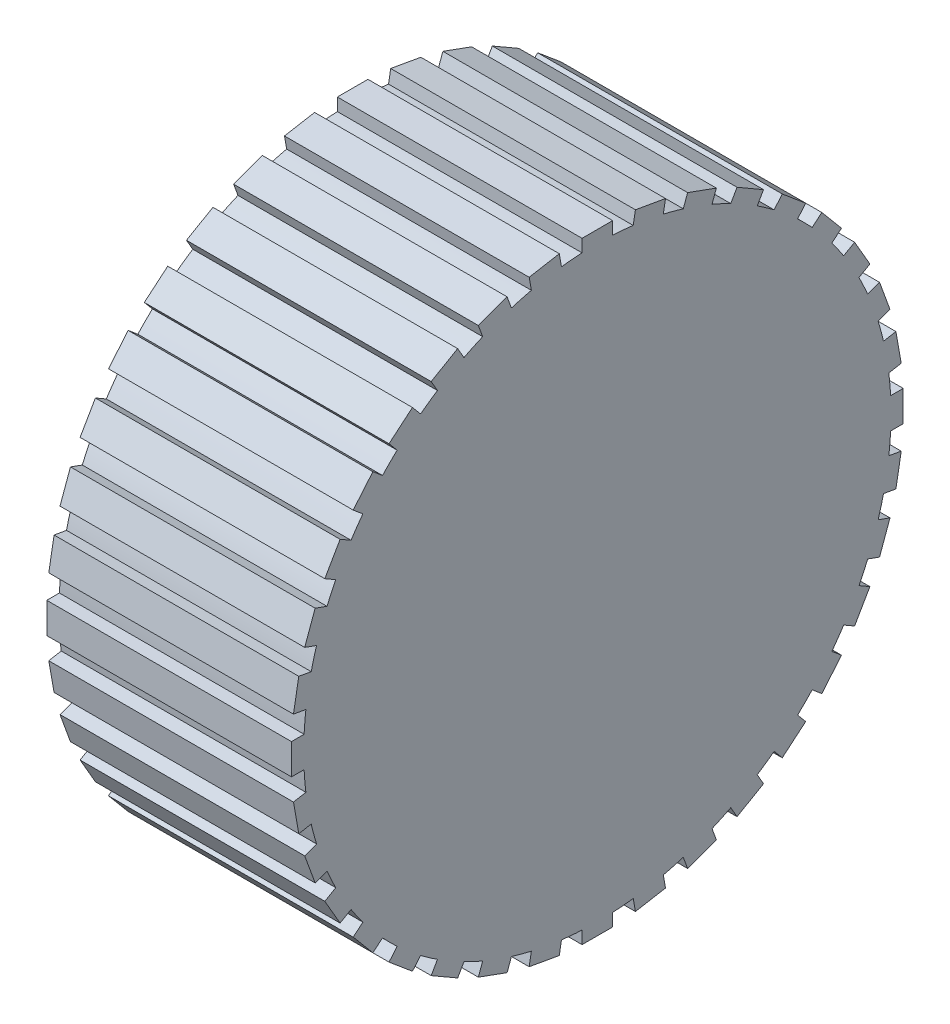
SolidWorks part; units mm, degrees
ref_plane "Front Plane" through (0, 0, 0) normal (0, 0, 1) x (1, 0, 0)
ref_plane "Top Plane" through (0, 0, 0) normal (0, 1, 0) x (1, 0, 0)
ref_plane "Right Plane" through (0, 0, 0) normal (1, 0, 0) x (0, 0, -1)
sketch "Sketch1" plane through (0, 0, 0) normal (1, 0, 0) x (0, 0, -1)
  line L0 (0, 0) -> (0, 250) construction
  line L1 (-12.5, 250) -> (12.5, 250)
  line L2 (-12.5, 250) -> (-12.5, 239.6743)
  line L3 (12.5, 250) -> (12.5, 239.6743)
  line L4 (31.1019, 248.3725) -> (55.7221, 244.0313)
  line L5 (31.1019, 248.3725) -> (29.3089, 238.2037)
  line L6 (55.7221, 244.0313) -> (53.9291, 233.8625)
  line L7 (73.7589, 239.1984) -> (97.2512, 230.6479)
  line L8 (73.7589, 239.1984) -> (70.2273, 229.4954)
  line L9 (97.2512, 230.6479) -> (93.7196, 220.9449)
  line L10 (114.1747, 222.7564) -> (135.8253, 210.2564)
  line L11 (114.1747, 222.7564) -> (109.0118, 213.814)
  line L12 (135.8253, 210.2564) -> (130.6624, 201.314)
  line L13 (151.1213, 199.546) -> (170.2725, 183.4763)
  line L14 (151.1213, 199.546) -> (144.4841, 191.636)
  line L15 (170.2725, 183.4763) -> (163.6352, 175.5663)
  line L16 (183.4763, 170.2725) -> (199.546, 151.1213)
  line L17 (183.4763, 170.2725) -> (175.5663, 163.6352)
  line L18 (199.546, 151.1213) -> (191.636, 144.4841)
  line L19 (210.2564, 135.8253) -> (222.7564, 114.1747)
  line L20 (210.2564, 135.8253) -> (201.314, 130.6624)
  line L21 (222.7564, 114.1747) -> (213.814, 109.0118)
  line L22 (230.6479, 97.2512) -> (239.1984, 73.7589)
  line L23 (230.6479, 97.2512) -> (220.9449, 93.7196)
  line L24 (239.1984, 73.7589) -> (229.4954, 70.2273)
  line L25 (244.0313, 55.7221) -> (248.3725, 31.1019)
  line L26 (244.0313, 55.7221) -> (233.8625, 53.9291)
  line L27 (248.3725, 31.1019) -> (238.2037, 29.3089)
  line L28 (250, 12.5) -> (250, -12.5)
  line L29 (250, 12.5) -> (239.6743, 12.5)
  line L30 (250, -12.5) -> (239.6743, -12.5)
  line L31 (248.3725, -31.1019) -> (244.0313, -55.7221)
  line L32 (248.3725, -31.1019) -> (238.2037, -29.3089)
  line L33 (244.0313, -55.7221) -> (233.8625, -53.9291)
  line L34 (239.1984, -73.7589) -> (230.6479, -97.2512)
  line L35 (239.1984, -73.7589) -> (229.4954, -70.2273)
  line L36 (230.6479, -97.2512) -> (220.9449, -93.7196)
  line L37 (222.7564, -114.1747) -> (210.2564, -135.8253)
  line L38 (222.7564, -114.1747) -> (213.814, -109.0118)
  line L39 (210.2564, -135.8253) -> (201.314, -130.6624)
  line L40 (199.546, -151.1213) -> (183.4763, -170.2725)
  line L41 (199.546, -151.1213) -> (191.636, -144.4841)
  line L42 (183.4763, -170.2725) -> (175.5663, -163.6352)
  line L43 (170.2725, -183.4763) -> (151.1213, -199.546)
  line L44 (170.2725, -183.4763) -> (163.6352, -175.5663)
  line L45 (151.1213, -199.546) -> (144.4841, -191.636)
  line L46 (135.8253, -210.2564) -> (114.1747, -222.7564)
  line L47 (135.8253, -210.2564) -> (130.6624, -201.314)
  line L48 (114.1747, -222.7564) -> (109.0118, -213.814)
  line L49 (97.2512, -230.6479) -> (73.7589, -239.1984)
  line L50 (97.2512, -230.6479) -> (93.7196, -220.9449)
  line L51 (73.7589, -239.1984) -> (70.2273, -229.4954)
  line L52 (55.7221, -244.0313) -> (31.1019, -248.3725)
  line L53 (55.7221, -244.0313) -> (53.9291, -233.8625)
  line L54 (31.1019, -248.3725) -> (29.3089, -238.2037)
  line L55 (12.5, -250) -> (-12.5, -250)
  line L56 (12.5, -250) -> (12.5, -239.6743)
  line L57 (-12.5, -250) -> (-12.5, -239.6743)
  line L58 (-31.1019, -248.3725) -> (-55.7221, -244.0313)
  line L59 (-31.1019, -248.3725) -> (-29.3089, -238.2037)
  line L60 (-55.7221, -244.0313) -> (-53.9291, -233.8625)
  line L61 (-73.7589, -239.1984) -> (-97.2512, -230.6479)
  line L62 (-73.7589, -239.1984) -> (-70.2273, -229.4954)
  line L63 (-97.2512, -230.6479) -> (-93.7196, -220.9449)
  line L64 (-114.1747, -222.7564) -> (-135.8253, -210.2564)
  line L65 (-114.1747, -222.7564) -> (-109.0118, -213.814)
  line L66 (-135.8253, -210.2564) -> (-130.6624, -201.314)
  line L67 (-151.1213, -199.546) -> (-170.2725, -183.4763)
  line L68 (-151.1213, -199.546) -> (-144.4841, -191.636)
  line L69 (-170.2725, -183.4763) -> (-163.6352, -175.5663)
  line L70 (-183.4763, -170.2725) -> (-199.546, -151.1213)
  line L71 (-183.4763, -170.2725) -> (-175.5663, -163.6352)
  line L72 (-199.546, -151.1213) -> (-191.636, -144.4841)
  line L73 (-210.2564, -135.8253) -> (-222.7564, -114.1747)
  line L74 (-210.2564, -135.8253) -> (-201.314, -130.6624)
  line L75 (-222.7564, -114.1747) -> (-213.814, -109.0118)
  line L76 (-230.6479, -97.2512) -> (-239.1984, -73.7589)
  line L77 (-230.6479, -97.2512) -> (-220.9449, -93.7196)
  line L78 (-239.1984, -73.7589) -> (-229.4954, -70.2273)
  line L79 (-244.0313, -55.7221) -> (-248.3725, -31.1019)
  line L80 (-244.0313, -55.7221) -> (-233.8625, -53.9291)
  line L81 (-248.3725, -31.1019) -> (-238.2037, -29.3089)
  line L82 (-250, -12.5) -> (-250, 12.5)
  line L83 (-250, -12.5) -> (-239.6743, -12.5)
  line L84 (-250, 12.5) -> (-239.6743, 12.5)
  line L85 (-248.3725, 31.1019) -> (-244.0313, 55.7221)
  line L86 (-248.3725, 31.1019) -> (-238.2037, 29.3089)
  line L87 (-244.0313, 55.7221) -> (-233.8625, 53.9291)
  line L88 (-239.1984, 73.7589) -> (-230.6479, 97.2512)
  line L89 (-239.1984, 73.7589) -> (-229.4954, 70.2273)
  line L90 (-230.6479, 97.2512) -> (-220.9449, 93.7196)
  line L91 (-222.7564, 114.1747) -> (-210.2564, 135.8253)
  line L92 (-222.7564, 114.1747) -> (-213.814, 109.0118)
  line L93 (-210.2564, 135.8253) -> (-201.314, 130.6624)
  line L94 (-199.546, 151.1213) -> (-183.4763, 170.2725)
  line L95 (-199.546, 151.1213) -> (-191.636, 144.4841)
  line L96 (-183.4763, 170.2725) -> (-175.5663, 163.6352)
  line L97 (-170.2725, 183.4763) -> (-151.1213, 199.546)
  line L98 (-170.2725, 183.4763) -> (-163.6352, 175.5663)
  line L99 (-151.1213, 199.546) -> (-144.4841, 191.636)
  line L100 (-135.8253, 210.2564) -> (-114.1747, 222.7564)
  line L101 (-135.8253, 210.2564) -> (-130.6624, 201.314)
  line L102 (-114.1747, 222.7564) -> (-109.0118, 213.814)
  line L103 (-97.2512, 230.6479) -> (-73.7589, 239.1984)
  line L104 (-97.2512, 230.6479) -> (-93.7196, 220.9449)
  line L105 (-73.7589, 239.1984) -> (-70.2273, 229.4954)
  line L106 (-55.7221, 244.0313) -> (-31.1019, 248.3725)
  line L107 (-55.7221, 244.0313) -> (-53.9291, 233.8625)
  line L108 (-31.1019, 248.3725) -> (-29.3089, 238.2037)
  circle A0 centre (0, 0) radius 250 construction
  arc A1 (-12.5, 239.6743) -> (-29.3089, 238.2037) centre (0, 0) ccw
  arc A2 (29.3089, 238.2037) -> (12.5, 239.6743) centre (0, 0) ccw
  arc A3 (70.2273, 229.4954) -> (53.9291, 233.8625) centre (0, 0) ccw
  arc A4 (109.0118, 213.814) -> (93.7196, 220.9449) centre (0, 0) ccw
  arc A5 (144.4841, 191.636) -> (130.6624, 201.314) centre (0, 0) ccw
  arc A6 (175.5663, 163.6352) -> (163.6352, 175.5663) centre (0, 0) ccw
  arc A7 (201.314, 130.6624) -> (191.636, 144.4841) centre (0, 0) ccw
  arc A8 (220.9449, 93.7196) -> (213.814, 109.0118) centre (0, 0) ccw
  arc A9 (233.8625, 53.9291) -> (229.4954, 70.2273) centre (0, 0) ccw
  arc A10 (239.6743, 12.5) -> (238.2037, 29.3089) centre (0, 0) ccw
  arc A11 (238.2037, -29.3089) -> (239.6743, -12.5) centre (0, 0) ccw
  arc A12 (229.4954, -70.2273) -> (233.8625, -53.9291) centre (0, 0) ccw
  arc A13 (213.814, -109.0118) -> (220.9449, -93.7196) centre (0, 0) ccw
  arc A14 (191.636, -144.4841) -> (201.314, -130.6624) centre (0, 0) ccw
  arc A15 (163.6352, -175.5663) -> (175.5663, -163.6352) centre (0, 0) ccw
  arc A16 (130.6624, -201.314) -> (144.4841, -191.636) centre (0, 0) ccw
  arc A17 (93.7196, -220.9449) -> (109.0118, -213.814) centre (0, 0) ccw
  arc A18 (53.9291, -233.8625) -> (70.2273, -229.4954) centre (0, 0) ccw
  arc A19 (12.5, -239.6743) -> (29.3089, -238.2037) centre (0, 0) ccw
  arc A20 (-29.3089, -238.2037) -> (-12.5, -239.6743) centre (0, 0) ccw
  arc A21 (-70.2273, -229.4954) -> (-53.9291, -233.8625) centre (0, 0) ccw
  arc A22 (-109.0118, -213.814) -> (-93.7196, -220.9449) centre (0, 0) ccw
  arc A23 (-144.4841, -191.636) -> (-130.6624, -201.314) centre (0, 0) ccw
  arc A24 (-175.5663, -163.6352) -> (-163.6352, -175.5663) centre (0, 0) ccw
  arc A25 (-220.9449, -93.7196) -> (-213.814, -109.0118) centre (0, 0) ccw
  arc A26 (-201.314, -130.6624) -> (-191.636, -144.4841) centre (0, 0) ccw
  arc A27 (-233.8625, -53.9291) -> (-229.4954, -70.2273) centre (0, 0) ccw
  arc A28 (-239.6743, -12.5) -> (-238.2037, -29.3089) centre (0, 0) ccw
  arc A29 (-238.2037, 29.3089) -> (-239.6743, 12.5) centre (0, 0) ccw
  arc A30 (-229.4954, 70.2273) -> (-233.8625, 53.9291) centre (0, 0) ccw
  arc A31 (-213.814, 109.0118) -> (-220.9449, 93.7196) centre (0, 0) ccw
  arc A32 (-191.636, 144.4841) -> (-201.314, 130.6624) centre (0, 0) ccw
  arc A33 (-163.6352, 175.5663) -> (-175.5663, 163.6352) centre (0, 0) ccw
  arc A34 (-130.6624, 201.314) -> (-144.4841, 191.636) centre (0, 0) ccw
  arc A35 (-53.9291, 233.8625) -> (-70.2273, 229.4954) centre (0, 0) ccw
  arc A36 (-93.7196, 220.9449) -> (-109.0118, 213.814) centre (0, 0) ccw
  point P152 (0, 0)
  dimension "D1" = 500
  dimension "D2" = 36
  dimension "D3" = 480
  dimension "D4" = 10.3257
extrude "Boss-Extrude1" add sketch "Sketch1" along normal blind 200
sketch "Sketch2" plane through (0, 0, 0) normal (-1, 0, 0) x (0, 0, 1)
  circle A0 centre (0, 0) radius 50
  dimension "D1" = 100
extrude "Cut-Extrude1" cut sketch "Sketch2" against normal blind 100
